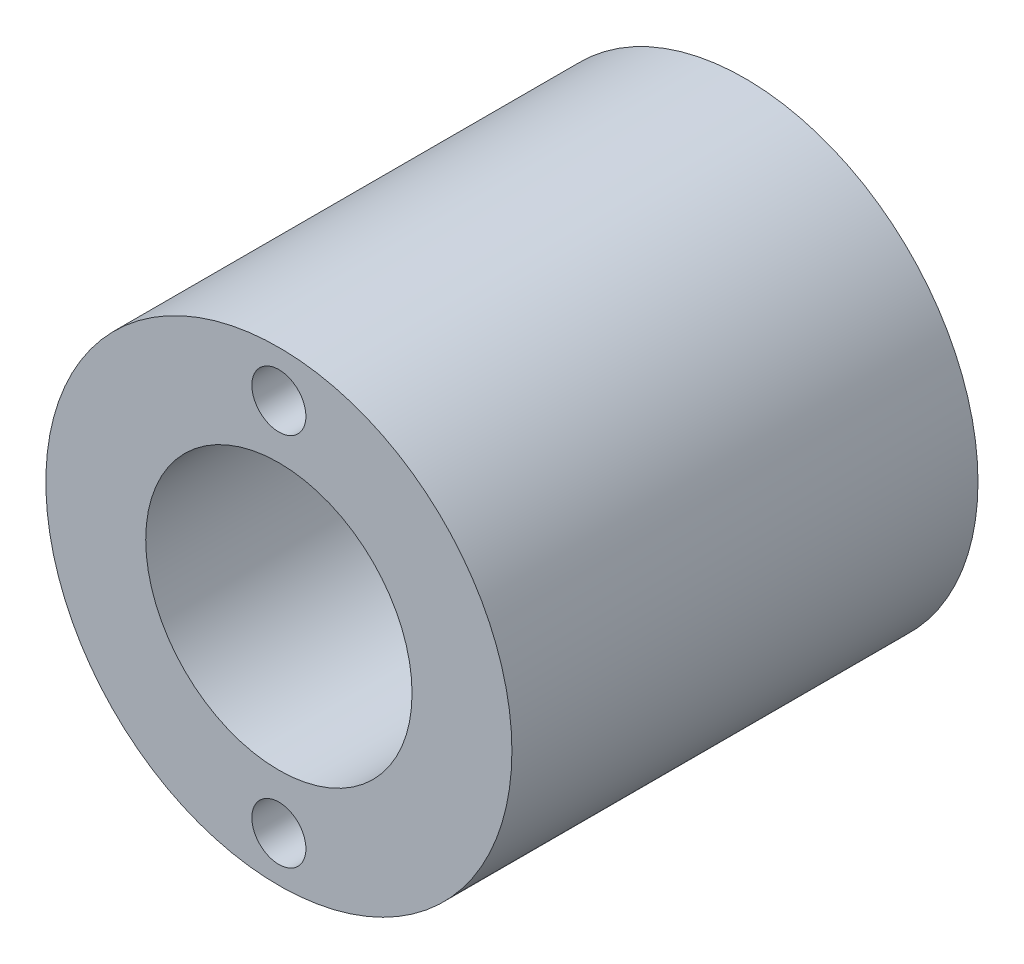
SolidWorks part; units mm, degrees
ref_plane "Front Plane" through (0, 0, 0) normal (0, 0, 1) x (1, 0, 0)
ref_plane "Top Plane" through (0, 0, 0) normal (0, 1, 0) x (1, 0, 0)
ref_plane "Right Plane" through (0, 0, 0) normal (1, 0, 0) x (0, 0, -1)
sketch "Sketch1" plane through (0, 0, 0) normal (0, 0, 1) x (1, 0, 0)
  line L0 (0, 28.6378) -> (0, -45.7992) construction
  circle A0 centre (0, 0) radius 22.225
  circle A1 centre (0, 0) radius 12.7
  circle A2 centre (0, 17.8117) radius 2.5781
  circle A3 centre (0, -17.907) radius 2.5781
  dimension "D1" = 25.4
  dimension "D2" = 44.45
  dimension "D3" = 5.1562
  dimension "D4" = 5.1562
  dimension "D5" = 35.7188
  dimension "D6" = 17.907
  dimension "D7" = 44.45
  dimension "D8" = 17.8117
extrude "Boss-Extrude1" add sketch "Sketch1" along normal blind 44.45
sketch "Sketch2" plane through (0, 0, 0) normal (1, 0, 0) x (0, 0, -1)
  line L0 (0, -22.225) -> (0, 22.225) construction
  circle A0 centre (-8.89, 0) radius 6.35
  dimension "D1" = 8.89
  dimension "D2" = 12.7
  dimension "D3" = 8.89
extrude "Cut-Extrude1" cut sketch "Sketch2" against normal blind 44.45
